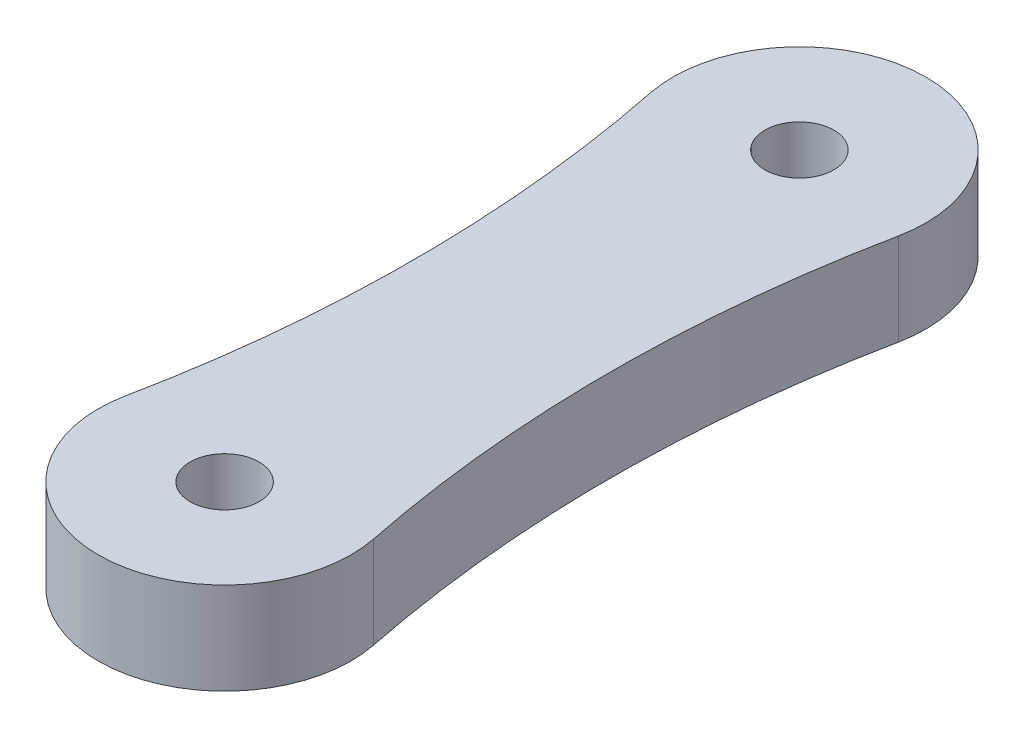
SolidWorks part; units mm, degrees
ref_plane "Front Plane" through (0, 0, 0) normal (0, 0, 1) x (1, 0, 0)
ref_plane "Top Plane" through (0, 0, 0) normal (0, 1, 0) x (1, 0, 0)
ref_plane "Right Plane" through (0, 0, 0) normal (1, 0, 0) x (0, 0, -1)
sketch "Sketch1" plane through (0, 0, 0) normal (0, 1, 0) x (1, 0, 0)
  line L0 (0, 0) -> (0, 25) construction
  line L3 (-4.25, 12.5) -> (4.25, 12.5) construction
  circle A2 centre (0, 0) radius 1.5
  circle A3 centre (0, 25) radius 1.5
  arc A8 (-5.3911, 1.0891) -> (5.3911, 1.0891) centre (0, 0) ccw
  arc A9 (5.3911, 23.9109) -> (-5.3911, 23.9109) centre (0, 25) ccw
  arc A10 (-5.3911, 23.9109) -> (-5.3911, 1.0891) centre (-61.875, 12.5) cw
  arc A11 (5.3911, 23.9109) -> (5.3911, 1.0891) centre (61.875, 12.5) ccw
  point P3 (0, 12.5)
  point P16 (-4.25, 12.5)
  point P17 (0, 0)
  point P18 (0, 0)
  point P19 (4.25, 12.5)
  point P23 (0, 12.5)
  dimension "D1" = 3
  dimension "D2" = 25
  dimension "D3" = 4
  dimension "D4" = 8.5
extrude "Boss-Extrude1" add sketch "Sketch1" along normal blind 4
